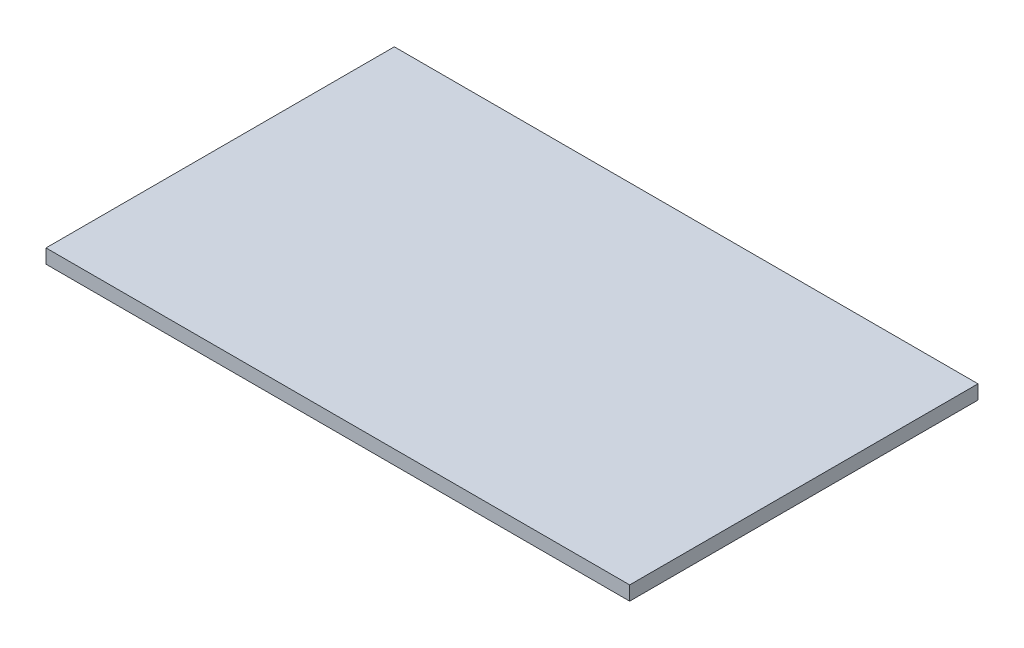
SolidWorks part; units mm, degrees
material "Melamine resin"
ref_plane "Front Plane" through (0, 0, 0) normal (0, 0, 1) x (1, 0, 0)
ref_plane "Top Plane" through (0, 0, 0) normal (0, 1, 0) x (1, 0, 0)
ref_plane "Right Plane" through (0, 0, 0) normal (1, 0, 0) x (0, 0, -1)
sketch "Sketch1" plane through (0, 0, 0) normal (0, 1, 0) x (1, 0, 0)
  line L1 (0, 0) -> (62, 0)
  line L2 (0, 0) -> (0, 37)
  line L3 (0, 37) -> (62, 37)
  line L4 (62, 0) -> (62, 37)
  dimension "D1" = 37
  dimension "D2" = 62
extrude "Boss-Extrude1" add sketch "Sketch1" along normal blind 1.5
